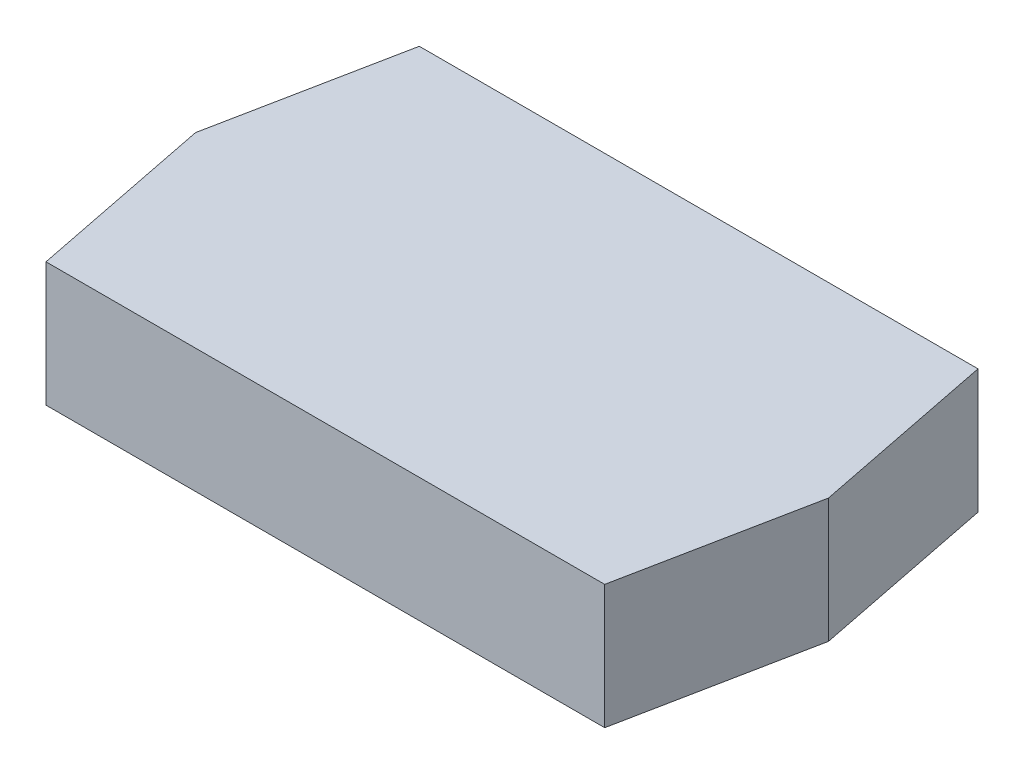
SolidWorks part; units mm, degrees
ref_plane "Front Plane" through (0, 0, 0) normal (0, 0, 1) x (1, 0, 0)
ref_plane "Top Plane" through (0, 0, 0) normal (0, 1, 0) x (1, 0, 0)
ref_plane "Right Plane" through (0, 0, 0) normal (1, 0, 0) x (0, 0, -1)
sketch "Sketch1" plane through (0, 0, 0) normal (0, 1, 0) x (1, 0, 0)
  line L0 (-17.6777, -17.6777) -> (17.6777, 17.6777) construction
  line L9 (-10.3553, 25) -> (-25, 10.3553) construction
  line L10 (-25, 10.3553) -> (-25, -10.3553) construction
  line L11 (-25, -10.3553) -> (-10.3553, -25) construction
  line L12 (-10.3553, -25) -> (10.3553, -25) construction
  line L13 (10.3553, -25) -> (25, -10.3553) construction
  line L22 (25, -10.3553) -> (25, 10.3553) construction
  line L23 (25, 10.3553) -> (10.3553, 25) construction
  line L24 (10.3553, 25) -> (-10.3553, 25) construction
  line L25 (0, 0) -> (25, 0) construction
  line L26 (0, 0) -> (23.097, 9.5671) construction
  line L27 (0, 0) -> (24.5196, 4.8773) construction
  line L28 (0, 0) -> (20.7867, 13.8893) construction
  line L29 (0, 0) -> (13.8893, 20.7867) construction
  line L30 (0, 0) -> (9.5671, 23.097) construction
  line L31 (22.4994, 15.0336) -> (25.4898, 0)
  line L32 (22.4994, 15.0336) -> (-22.4994, 15.0336)
  line L33 (-22.4994, 15.0336) -> (-25.4898, 0)
  line L34 (25.4898, 0) -> (22.4994, -15.0336)
  line L35 (22.4994, -15.0336) -> (-22.4994, -15.0336)
  line L36 (-22.4994, -15.0336) -> (-25.4898, 0)
  line L37 (0, 0) -> (-24.5196, -4.8773) construction
  circle A2 centre (0, 0) radius 25 construction
  circle A3 centre (0, 0) radius 27.0598 construction
  dimension "D1" = 50
  dimension "D2" = 22.5
  dimension "D3" = 11.25
  dimension "D4" = 11.25
  dimension "D5" = 11.25
  dimension "D6" = 11.25
extrude "Boss-Extrude1" add sketch "Sketch1" along normal blind 10
